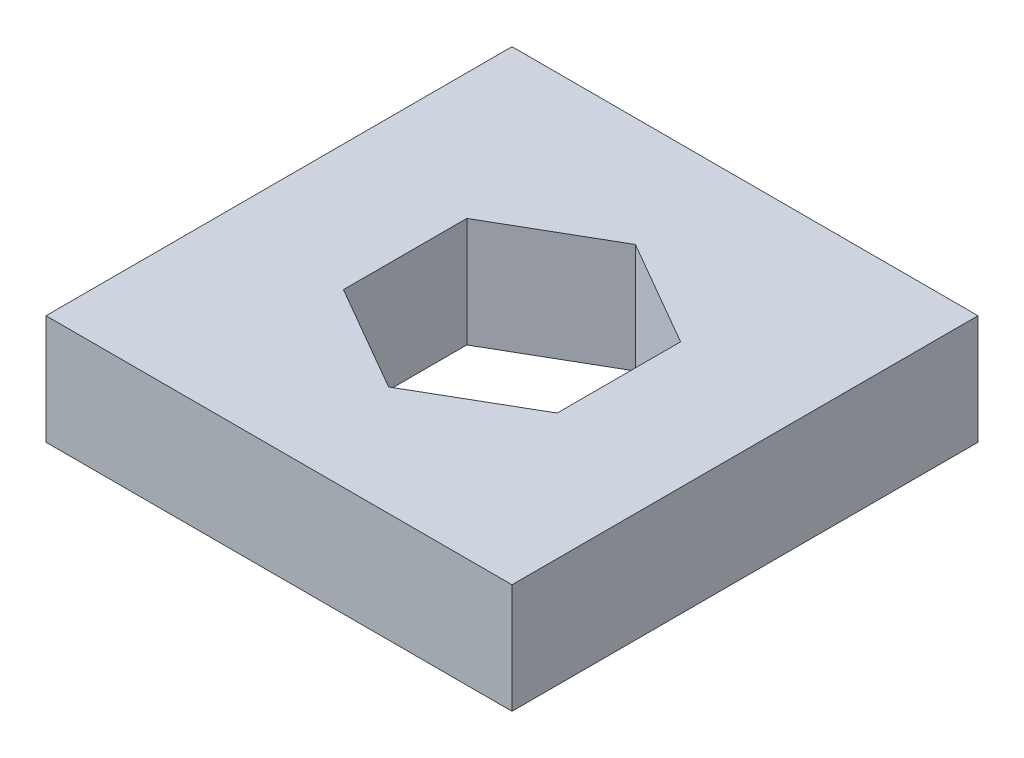
SolidWorks part; units mm, degrees
ref_plane "Front Plane" through (0, 0, 0) normal (0, 0, 1) x (1, 0, 0)
ref_plane "Top Plane" through (0, 0, 0) normal (0, 1, 0) x (1, 0, 0)
ref_plane "Right Plane" through (0, 0, 0) normal (1, 0, 0) x (0, 0, -1)
sketch "Sketch1" plane through (0, 0, 0) normal (0, 1, 0) x (1, 0, 0)
  line L1 (0, 7.149) -> (-6.1913, 3.5745)
  line L2 (-6.1913, 3.5745) -> (-6.1912, -3.5745)
  line L3 (-6.1912, -3.5745) -> (0, -7.149)
  line L4 (0, -7.149) -> (6.1913, -3.5745)
  line L5 (6.1913, -3.5745) -> (6.1912, 3.5745)
  line L6 (6.1912, 3.5745) -> (0, 7.149)
  line L7 (-13.499, -13.499) -> (13.499, -13.499)
  line L8 (-13.499, -13.499) -> (-13.499, 13.499)
  line L9 (-13.499, 13.499) -> (13.499, 13.499)
  line L10 (13.499, -13.499) -> (13.499, 13.499)
  line L11 (-13.499, -13.499) -> (13.499, 13.499) construction
  line L12 (-13.499, 13.499) -> (13.499, -13.499) construction
  circle A0 centre (0, 0) radius 6.1913 construction
  point P1 (-3.0956, -5.3618)
  dimension "D1" = 12.3825
  dimension "D2" = 6.35
extrude "Boss-Extrude1" add sketch "Sketch1" against normal blind 6.35 contours L7 L10 L9 L8 L6 L5 L4 L3 L2 L1
